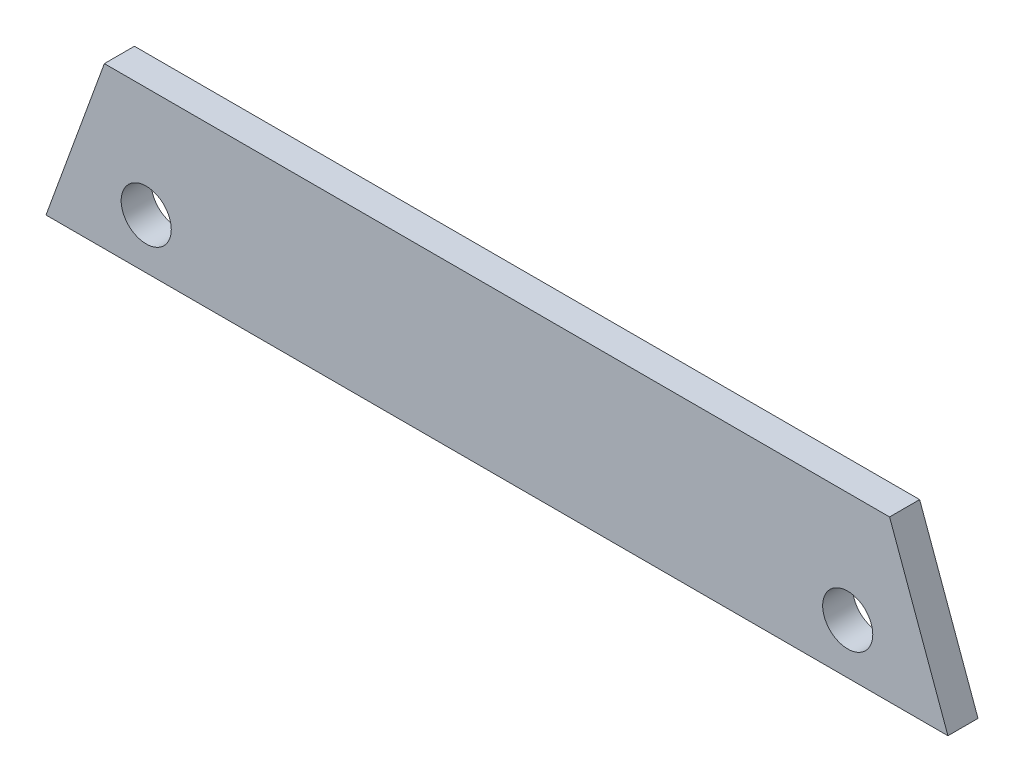
SolidWorks part; units mm, degrees
ref_plane "Alzado" through (0, 0, 0) normal (0, 0, 1) x (1, 0, 0)
ref_plane "Planta" through (0, 0, 0) normal (0, 1, 0) x (1, 0, 0)
ref_plane "Vista lateral" through (0, 0, 0) normal (1, 0, 0) x (0, 0, -1)
sketch "Croquis1" plane through (0, 0, 0) normal (0, 0, 1) x (1, 0, 0)
  line L0 (-45, 0) -> (45, 0)
  line L1 (45, 0) -> (39.1765, 16)
  line L2 (39.1765, 16) -> (-39.1765, 16)
  line L3 (-39.1765, 16) -> (-45, 0)
  circle A0 centre (-35, 5) radius 2.5
  circle A1 centre (35, 5) radius 2.5
  point P9 (0, 0)
  dimension "D6" = 5
  dimension "D1" = 16
  dimension "D2" = 90
  dimension "D3" = 45
  dimension "D4" = 70
  dimension "D5" = 70
  dimension "D7" = 5
  dimension "D8" = 10
  dimension "D9" = 10
extrude "Saliente-Extruir1" add sketch "Croquis1" along normal blind 3
